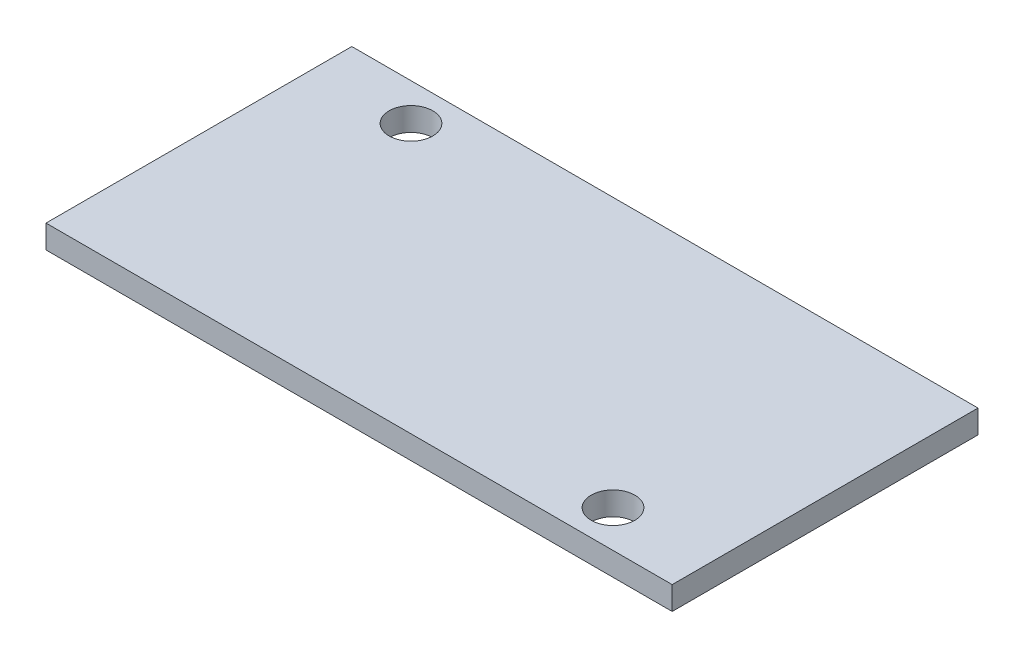
SolidWorks part; units mm, degrees
ref_plane "Front Plane" through (0, 0, 0) normal (0, 0, 1) x (1, 0, 0)
ref_plane "Top Plane" through (0, 0, 0) normal (0, 1, 0) x (1, 0, 0)
ref_plane "Right Plane" through (0, 0, 0) normal (1, 0, 0) x (0, 0, -1)
sketch "Sketch1" plane through (0, 0, 0) normal (0, 1, 0) x (1, 0, 0)
  line L0 (-23.8195, 10.9624) -> (-17.2155, 10.9624) construction
  line L1 (-23.8195, 21.4624) -> (19.1805, 21.4624)
  line L2 (-23.8195, 21.4624) -> (-23.8195, 0.4624)
  line L3 (-23.8195, 0.4624) -> (19.1805, 0.4624)
  line L4 (19.1805, 21.4624) -> (19.1805, 0.4624)
  line L5 (-17.2155, 21.4624) -> (-17.2155, 18.9224) construction
  line L6 (-2.3195, 21.4624) -> (-2.3195, 20.4624) construction
  line L7 (-2.3195, 0.4624) -> (-2.3195, 1.4624) construction
  line L8 (-16.8195, 1.4624) -> (12.1805, 20.4624) construction
  line L9 (19.1805, 10.9624) -> (12.5765, 10.9624) construction
  line L10 (12.5765, 0.4624) -> (12.5765, 3.0024) construction
  circle A0 centre (-17.2155, 18.9224) radius 1.5
  circle A1 centre (12.5765, 3.0024) radius 1.5
  dimension "D1" = 43
  dimension "D2" = 21
extrude "Boss-Extrude3" add sketch "Sketch1" along normal blind 1.6
